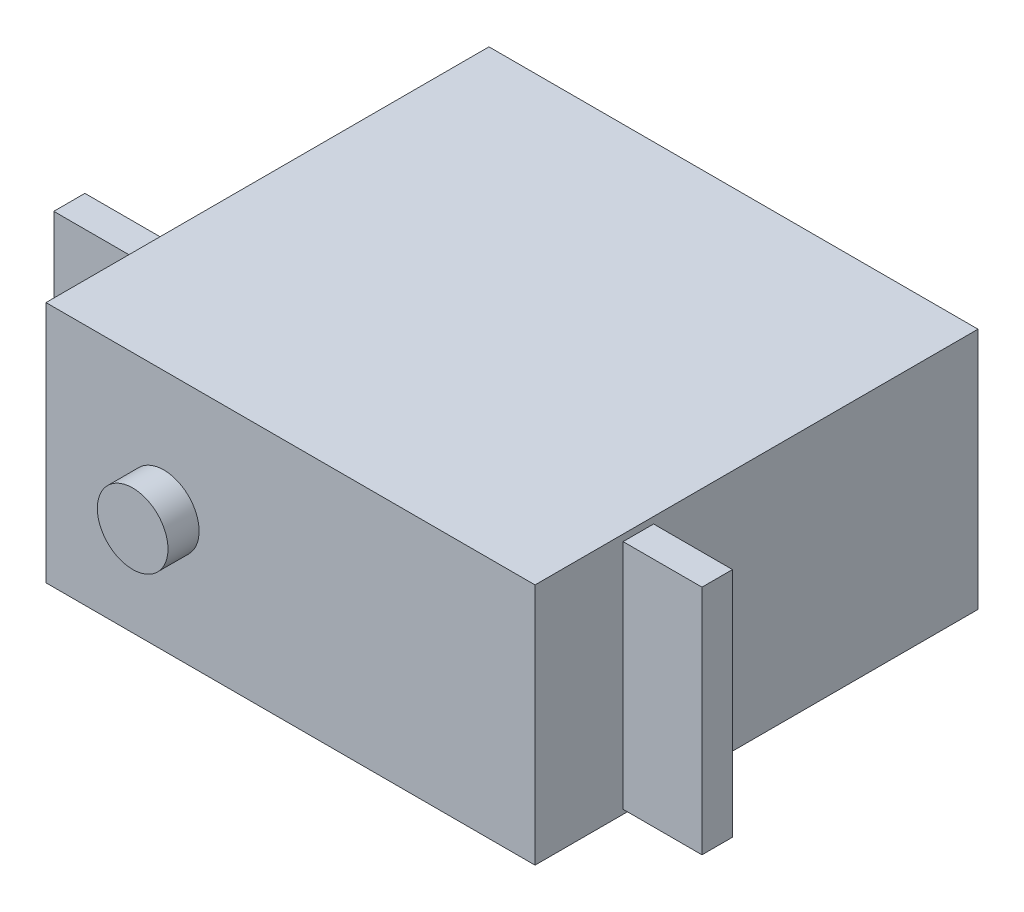
SolidWorks part; units mm, degrees
ref_plane "Front Plane" through (0, 0, 0) normal (0, 0, 1) x (1, 0, 0)
ref_plane "Top Plane" through (0, 0, 0) normal (0, 1, 0) x (1, 0, 0)
ref_plane "Right Plane" through (0, 0, 0) normal (1, 0, 0) x (0, 0, -1)
sketch "Sketch1" plane through (0, 0, 0) normal (0, 1, 0) x (1, 0, 0)
  line L1 (-39.9161, 0) -> (0, 0)
  line L2 (-39.9161, 0) -> (-39.9161, -36.1569)
  line L3 (-39.9161, -36.1569) -> (0, -36.1569)
  line L4 (0, 0) -> (0, -36.1569)
  dimension "D1" = 39.9161
  dimension "D2" = 36.1569
extrude "Boss-Extrude1" add sketch "Sketch1" along normal blind 19.812
sketch "Sketch2" plane through (0, 0, 0) normal (1, 0, 0) x (0, 0, -1)
  line L0 (-36.1569, 0) -> (0, 0) construction
  line L1 (-28.9687, 0.3556) -> (-26.4795, 0.3556)
  line L2 (-28.9687, 0.3556) -> (-28.9687, 19.2786)
  line L3 (-28.9687, 19.2786) -> (-26.4795, 19.2786)
  line L4 (-26.4795, 0.3556) -> (-26.4795, 19.2786)
  line L5 (-36.1569, 19.812) -> (-36.1569, 0) construction
  dimension "D1" = 18.923
  dimension "D2" = 2.4892
  dimension "D3" = 0.3556
  dimension "D4" = 7.1882
extrude "Boss-Extrude3" add sketch "Sketch2" along normal blind 6.4389
sketch "Sketch4" plane through (-39.9161, 0, 0) normal (-1, 0, 0) x (0, 0, 1)
  line L0 (0, 19.812) -> (36.1569, 19.812) construction
  line L1 (29.083, 19.5072) -> (26.543, 19.5072)
  line L2 (29.083, 19.5072) -> (29.083, 0.5842)
  line L3 (29.083, 0.5842) -> (26.543, 0.5842)
  line L4 (26.543, 19.5072) -> (26.543, 0.5842)
  line L5 (36.1569, 19.812) -> (36.1569, 0) construction
  dimension "D1" = 18.923
  dimension "D2" = 2.54
  dimension "D3" = 0.3048
  dimension "D4" = 7.0739
extrude "Boss-Extrude4" add sketch "Sketch4" along normal blind 6.4389
sketch "Sketch5" plane through (0, 0, 36.1569) normal (0, 0, 1) x (1, 0, 0)
  line L0 (-33.1851, 9.906) -> (-33.1851, 14.8784) construction
  line L1 (-39.9161, 19.812) -> (-39.9161, 0) construction
  line L2 (-39.9161, 0) -> (0, 0) construction
  line L3 (-39.9161, 19.812) -> (0, 19.812) construction
  circle A0 centre (-30.3022, 9.906) radius 2.8829
  dimension "D2" = 5.7658
  dimension "D3" = 9.906
  dimension "D1" = 6.731
  dimension "D4" = 9.906
extrude "Boss-Extrude5" add sketch "Sketch5" along normal blind 2.54
